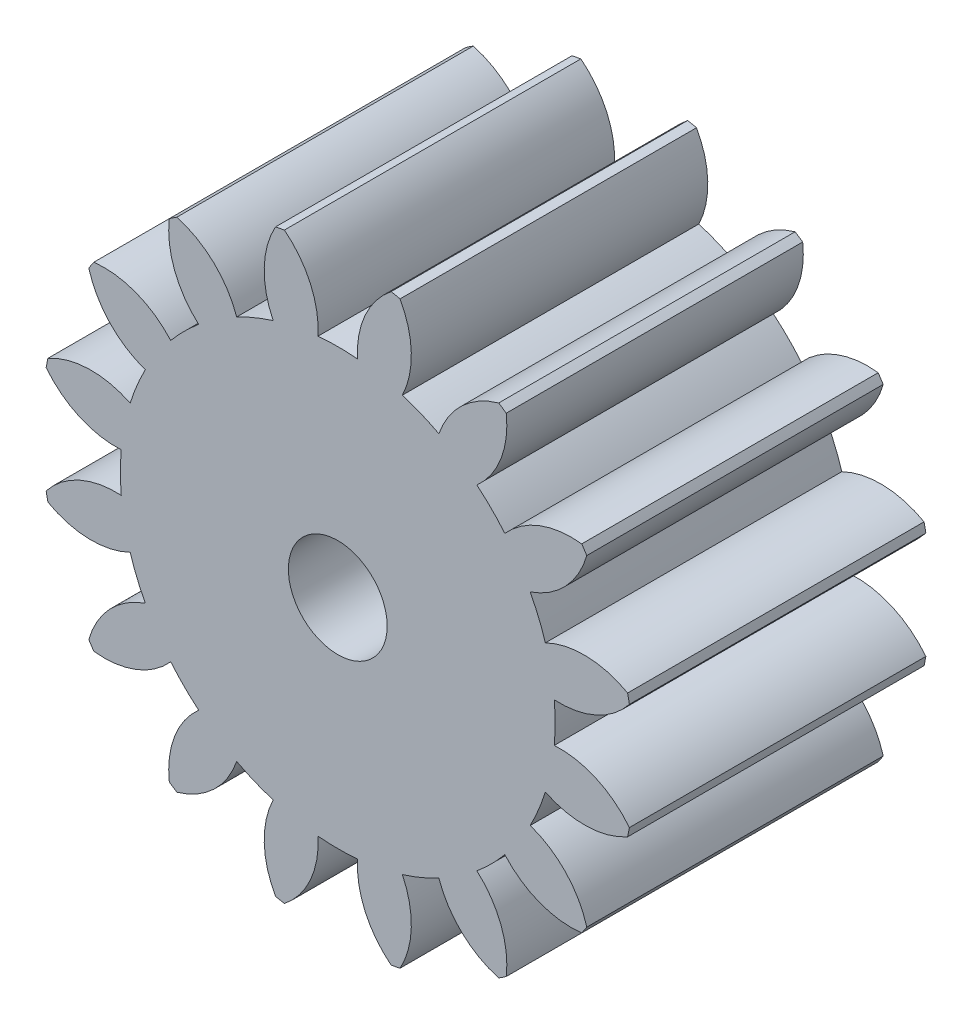
SolidWorks part; units mm, degrees
ref_plane "Front Plane" through (0, 0, 0) normal (0, 0, 1) x (1, 0, 0)
ref_plane "Top Plane" through (0, 0, 0) normal (0, 1, 0) x (1, 0, 0)
ref_plane "Right Plane" through (0, 0, 0) normal (1, 0, 0) x (0, 0, -1)
sketch "Sketch1" plane through (0, 0, 0) normal (0, 0, 1) x (1, 0, 0)
  circle A0 centre (0, 0) radius 15
  dimension "D1" = 30
extrude "Boss-Extrude1" add sketch "Sketch1" along normal blind 15
sketch "Sketch2" plane through (0, 0, 15) normal (0, 0, 1) x (1, 0, 0)
  line L0 (0, 15) -> (0, 11) construction
  arc A0 (-1, 10.9545) -> (1, 10.9545) centre (0, 0) cw
  arc A1 (-2.7, 14.755) -> (2.7, 14.755) centre (0, 0) cw
  circle A2 centre (0, 0) radius 15 construction
  arc A3 (-2.7, 14.755) -> (-1, 10.9545) centre (-5.4918, 11.2257) cw
  arc A4 (1, 10.9545) -> (2.7, 14.755) centre (5.4918, 11.2257) cw
  circle A5 centre (0, 0) radius 13 construction
  point P10 (0, 11)
  point P11 (0, 15)
  point P15 (0, 13)
  dimension "D1" = 11
  dimension "D2" = 4.5
  dimension "D3" = 5.4
  dimension "D4" = 2
extrude "Cut-Extrude1" cut sketch "Sketch2" against normal through all
pattern_circular "CirPattern1" count 16 over 360 about axis through (0, 0, 0) along (0, 0, 1) of "Cut-Extrude1"
sketch "Sketch3" plane through (0, 0, 15) normal (0, 0, 1) x (1, 0, 0)
  circle A0 centre (0, 0) radius 2.5
  dimension "D1" = 5
extrude "Cut-Extrude2" cut sketch "Sketch3" against normal through all contours A0
